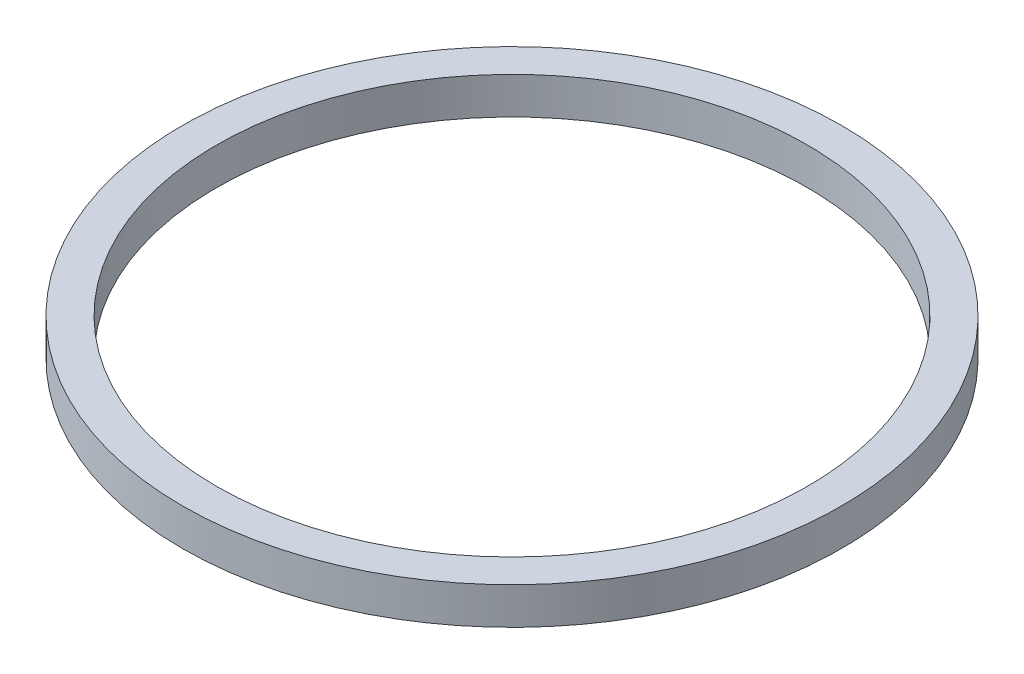
SolidWorks part; units mm, degrees
ref_plane "Front Plane" through (0, 0, 0) normal (0, 0, 1) x (1, 0, 0)
ref_plane "Top Plane" through (0, 0, 0) normal (0, 1, 0) x (1, 0, 0)
ref_plane "Right Plane" through (0, 0, 0) normal (1, 0, 0) x (0, 0, -1)
sketch "Sketch1" plane through (0, 0, 0) normal (0, 1, 0) x (1, 0, 0)
  circle A0 centre (0, 0) radius 12.7
  circle A1 centre (0, 0) radius 14.1605
  dimension "D1" = 25.4
  dimension "D2" = 28.321
extrude "Boss-Extrude1" add sketch "Sketch1" along normal blind 1.5875
